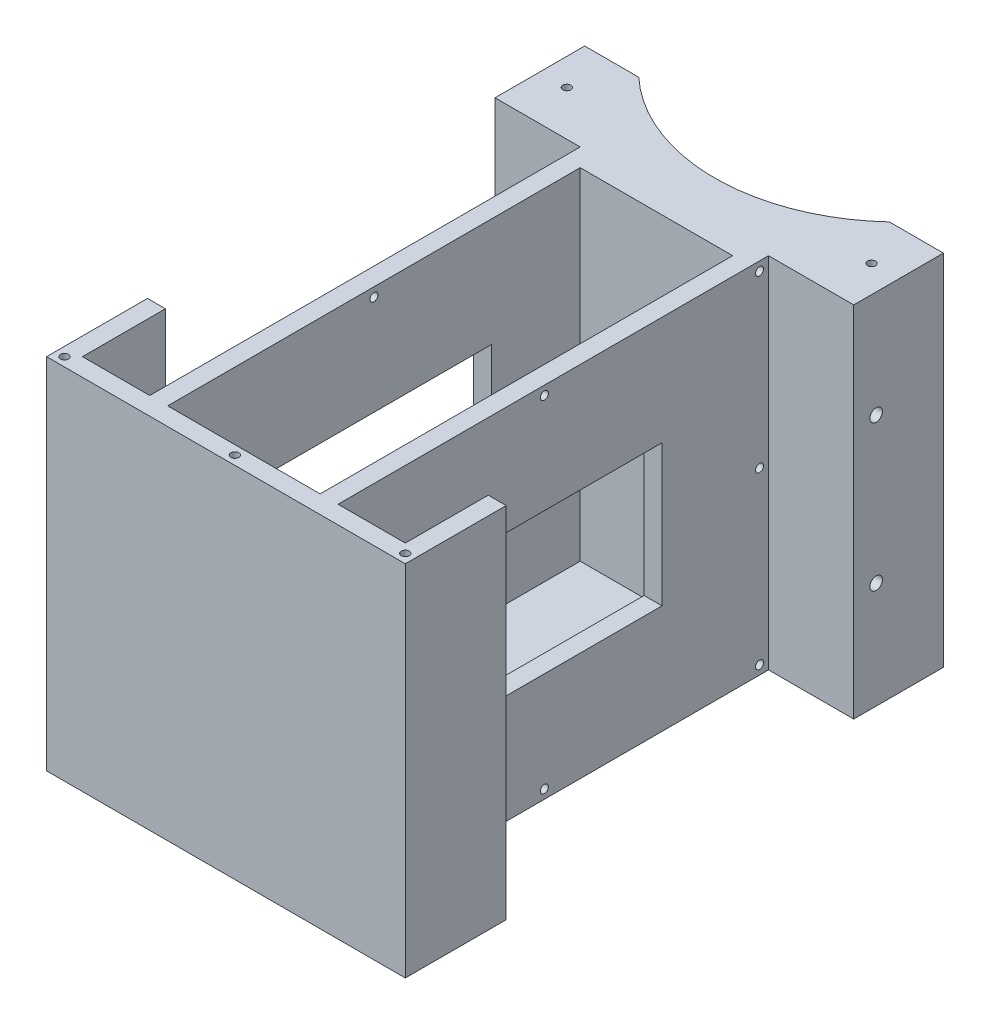
SolidWorks part; units mm, degrees
ref_plane "정면" through (0, 0, 0) normal (0, 0, 1) x (1, 0, 0)
ref_plane "윗면" through (0, 0, 0) normal (0, 1, 0) x (1, 0, 0)
ref_plane "우측면" through (0, 0, 0) normal (1, 0, 0) x (0, 0, -1)
ref_plane "평면1" through (0, 80, 0) normal (0, 1, 0) x (1, 0, 0)
sketch "스케치1" plane through (0, 80, 0) normal (0, 1, 0) x (1, 0, 0)
  line L0 (40, 60) -> (-40, 60)
  line L1 (-40, 60) -> (-40, -60)
  line L2 (-40, -60) -> (40, -60)
  line L3 (40, -60) -> (40, 60)
extrude "보스-돌출1" add sketch "스케치1" against normal blind 80
sketch "스케치2" plane through (0, 0, 0) normal (0, -1, 0) x (1, 0, 0)
  line L0 (-40, -40) -> (-21, -40)
  line L1 (-21, -40) -> (-21, 60)
  line L2 (-21, 60) -> (-40, 60)
  line L3 (-40, 60) -> (-40, -40)
extrude "컷-돌출1" cut sketch "스케치2" against normal through all
sketch "스케치3" plane through (0, 0, 0) normal (0, -1, 0) x (1, 0, 0)
  line L0 (21, 60) -> (21, -40)
  line L1 (21, -40) -> (40, -40)
  line L2 (40, -40) -> (40, 60)
  line L3 (40, 60) -> (21, 60)
extrude "컷-돌출2" cut sketch "스케치3" against normal through all
sketch "스케치4" plane through (0, 0, 0) normal (0, -1, 0) x (1, 0, 0)
  line L0 (-27.9464, -60) -> (27.9464, -60)
  arc A0 (27.9464, -60) -> (-27.9464, -60) centre (0, -90) ccw
extrude "컷-돌출3" cut sketch "스케치4" against normal through all
sketch "스케치5" plane through (0, 80, 0) normal (0, 1, 0) x (-1, 0, 0)
  line L0 (17, 56) -> (-17, 56)
  line L1 (-17, 56) -> (-17, -36)
  line L2 (-17, -36) -> (17, -36)
  line L3 (17, -36) -> (17, 56)
extrude "컷-돌출4" cut sketch "스케치5" against normal blind 76
sketch "스케치6" plane through (21, 0, 0) normal (1, 0, 0) x (0, 0, -1)
  line L0 (-34.75, 24.25) -> (14.75, 24.25)
  line L1 (14.75, 24.25) -> (14.75, 55.75)
  line L2 (14.75, 55.75) -> (-34.75, 55.75)
  line L3 (-34.75, 55.75) -> (-34.75, 24.25)
  line L4 (55, 80) -> (-55, 80) construction
  line L5 (40, 80) -> (40, 0) construction
  dimension "D1" = 31.5
  dimension "D2" = 49.5
  dimension "D3" = 24.25
  dimension "D4" = 25.25
extrude "컷-돌출5" cut sketch "스케치6" against normal up to next
sketch "스케치7" plane through (-21, 0, 0) normal (-1, 0, 0) x (0, 0, 1)
  line L0 (33.25, 55.75) -> (-16.25, 55.75)
  line L1 (-16.25, 55.75) -> (-16.25, 24.25)
  line L2 (-16.25, 24.25) -> (33.25, 24.25)
  line L3 (33.25, 24.25) -> (33.25, 55.75)
  line L4 (-40, 0) -> (60, 0) construction
  line L5 (-40, 80) -> (60, 80) construction
  line L7 (60, 80) -> (60, 0) construction
  dimension "D1" = 31.5
  dimension "D2" = 49.5
  dimension "D3" = 24.25
  dimension "D4" = 80
  dimension "D5" = 26.75
extrude "컷-돌출6" cut sketch "스케치7" against normal through all
hole_wizard "Ø1.8 (1.8) 지름 구멍5" positions "스케치9" profile "스케치8" hole size "Ø1.8" standard "Ansi Metric" end condition up to next
sketch "스케치9" plane through (-21, 0, 0) normal (-1, 0, 0) x (0, 0, 1)
  point P0 (10, 78)
sketch "스케치8" plane through (-21, 78, 10) normal (0, 1, 0) x (0, 0, 1)
  line L0 (0, 0) -> (0, 4)
  line L1 (0, 4) -> (0.9, 4)
  line L2 (0.9, 4) -> (0.9, 0)
  line L5 (0.9, 0) -> (0, 0)
  line L11 (0, -6.35) -> (0, 107.95) construction
  dimension "관통 구멍 지름" = 1.8
  dimension "관통 구멍 깊이" = 4
hole_wizard "Ø16.0 (16) 지름 구멍1" positions "스케치11" profile "스케치10" hole size "Ø16.0" standard "Ansi Metric" end condition through all
sketch "스케치11" plane through (0, 0, 0) normal (0, -1, 0) x (-1, 0, 0)
  point P0 (0, -22)
sketch "스케치10" plane through (0, 0, 22) normal (1, 0, 0) x (0, 0, -1)
  line L0 (0, 0) -> (0, 80)
  line L1 (0, 80) -> (8, 80)
  line L2 (8, 80) -> (8, 0)
  line L5 (8, 0) -> (0, 0)
  line L11 (0, -6.35) -> (0, 107.95) construction
  dimension "관통 구멍 지름" = 16
  dimension "관통 구멍 깊이" = 80
hole_wizard "Ø1.8 (1.8) 지름 구멍4" positions "스케치13" profile "스케치12" hole size "Ø1.8" standard "Ansi Metric"
sketch "스케치13" plane through (-21, 0, 0) normal (-1, 0, 0) x (0, 0, 1)
  point P0 (-38, 78)
  point P1 (-38, 40)
  point P2 (-38, 2)
  point P3 (10, 2)
sketch "스케치12" plane through (-21, 78, -38) normal (0, 1, 0) x (0, 0, 1)
  line L0 (0, 0) -> (0, 4.5408)
  line L1 (0, 4.5408) -> (0.9, 4)
  line L2 (0.9, 4) -> (0.9, 0)
  line L5 (0.9, 0) -> (0, 0)
  line L10 (0, 4.5408) -> (-0.9, 4) construction
  line L11 (0, -6.35) -> (0, 107.95) construction
  dimension "구멍 지름" = 1.8
  dimension "구멍 깊이" = 4
  dimension "드릴 각도" = 118
hole_wizard "Ø1.8 (1.8) 지름 구멍3" positions "스케치15" profile "스케치14" hole size "Ø1.8" standard "Ansi Metric" end condition through all
sketch "스케치15" plane through (21, 0, 0) normal (1, 0, 0) x (0, 0, -1)
  point P0 (-10, 78)
sketch "스케치14" plane through (21, 78, 10) normal (0, 1, 0) x (0, 0, -1)
  line L0 (0, 0) -> (0, 61)
  line L1 (0, 61) -> (0.9, 61)
  line L2 (0.9, 61) -> (0.9, 0)
  line L5 (0.9, 0) -> (0, 0)
  line L11 (0, -6.35) -> (0, 107.95) construction
  dimension "관통 구멍 지름" = 1.8
  dimension "관통 구멍 깊이" = 61
hole_wizard "Ø1.8 (1.8) 지름 구멍1" positions "스케치17" profile "스케치16" hole size "Ø1.8" standard "Ansi Metric"
sketch "스케치17" plane through (0, 80, 0) normal (0, 1, 0) x (1, 0, 0)
  point P0 (33.9732, 50)
  point P1 (-33.9732, 50)
sketch "스케치16" plane through (33.9732, 80, -50) normal (1, 0, 0) x (0, 0, 1)
  line L0 (0, 0) -> (0, 5.7408)
  line L1 (0, 5.7408) -> (0.9, 5.2)
  line L2 (0.9, 5.2) -> (0.9, 0)
  line L5 (0.9, 0) -> (0, 0)
  line L10 (0, 5.7408) -> (-0.9, 5.2) construction
  line L11 (0, -6.35) -> (0, 107.95) construction
  dimension "구멍 지름" = 1.8
  dimension "구멍 깊이" = 5.2
  dimension "드릴 각도" = 118
hole_wizard "Ø1.8 (1.8) 지름 구멍2" positions "스케치19" profile "스케치18" hole size "Ø1.8" standard "Ansi Metric"
sketch "스케치19" plane through (21, 0, 0) normal (1, 0, 0) x (0, 0, -1)
  point P0 (38, 78)
  point P1 (38, 40)
  point P2 (38, 2)
  point P3 (-10, 2)
sketch "스케치18" plane through (21, 78, -38) normal (0, 1, 0) x (0, 0, -1)
  line L0 (0, 0) -> (0, 4.5408)
  line L1 (0, 4.5408) -> (0.9, 4)
  line L2 (0.9, 4) -> (0.9, 0)
  line L5 (0.9, 0) -> (0, 0)
  line L10 (0, 4.5408) -> (-0.9, 4) construction
  line L11 (0, -6.35) -> (0, 107.95) construction
  dimension "구멍 지름" = 1.8
  dimension "구멍 깊이" = 4
  dimension "드릴 각도" = 118
sketch "스케치20" plane through (0, 80, 0) normal (0, 1, 0) x (1, 0, 0)
  line L0 (40, 40) -> (40, -101.7044) construction
  line L1 (-40, 60) -> (-40, 40) construction
  line L2 (21, -60) -> (55.4449, -60) construction
  line L3 (55.4449, -60) -> (-63.6399, -60) construction
  line L4 (40, 40) -> (40, 60) construction
  line L5 (40, -37.5) -> (36, -37.5)
  line L6 (40, -37.5) -> (40, -60)
  line L7 (40, -60) -> (-40, -60)
  line L8 (-40, -37.5) -> (-40, -60)
  line L9 (40, -37.5) -> (-40, -60) construction
  line L10 (40, -60) -> (-40, -37.5) construction
  line L12 (36, -37.5) -> (36, -56)
  line L13 (36, -56) -> (-36, -56)
  line L14 (-36, -56) -> (-36, -37.5)
  line L15 (-36, -37.5) -> (-40, -37.5)
  point P10 (0, -48.75)
  point P17 (40, 50)
  dimension "D1" = 0
  dimension "D2" = 80
  dimension "D3" = 0
  dimension "D4" = 4
  dimension "D5" = 4
  dimension "D6" = 4
  dimension "D7" = 22.5
  dimension "D8" = 22.5
  dimension "D9" = 80
extrude "보스-돌출2" add sketch "스케치20" against normal up to surface (80 mm away) up to face at (0, 0, -26.9)
sketch "스케치21" plane through (-40, 0, 0) normal (-1, 0, 0) x (0, 0, 1)
  line L0 (-40, 80) -> (-40, 0) construction
  line L1 (-50, 60) -> (-40, 60) construction
  line L2 (-50, 60) -> (-50, 20) construction
  line L3 (-50, 20) -> (-40, 20) construction
  line L4 (-40, 60) -> (-40, 20) construction
  line L5 (-60, 0) -> (-60, 80) construction
  circle A0 centre (23.2187, 40.5539) radius 22.5 construction
  circle A1 centre (-45, 23.75) radius 1.4
  circle A2 centre (-45, 56.25) radius 1.4
  point P8 (-50, 40)
  point P11 (-60, 40)
  point P18 (-46.7249, 20)
  dimension "D1" = 45
  dimension "D5" = 2.8
  dimension "D6" = 2.8
  dimension "D9" = 3.75
  dimension "D10" = 3.75
  dimension "D2" = 0
  dimension "D3" = 40
  dimension "D4" = 10
  dimension "D7" = 5
  dimension "D8" = 5
extrude "컷-돌출7" cut sketch "스케치21" against normal blind 8
sketch "스케치22" plane through (40, 0, 0) normal (1, 0, 0) x (0, 0, -1)
  line L0 (40, 80) -> (40, 0) construction
  line L1 (40, 20) -> (50, 20) construction
  line L2 (40, 20) -> (40, 60) construction
  line L3 (40, 60) -> (50, 60) construction
  line L4 (50, 20) -> (50, 60) construction
  line L5 (40, 0) -> (60, 0) construction
  circle A0 centre (45, 23.75) radius 1.4
  circle A1 centre (45, 56.25) radius 1.4
  dimension "D4" = 2.8
  dimension "D5" = 2.8
  dimension "D6" = 3.75
  dimension "D7" = 3.75
  dimension "D8" = 5
  dimension "D9" = 5
  dimension "D1" = 10
  dimension "D2" = 40
  dimension "D3" = 20
extrude "컷-돌출8" cut sketch "스케치22" against normal blind 8
sketch "스케치23" plane through (0, 80, 0) normal (0, 1, 0) x (1, 0, 0)
  line L0 (-40, -37.5) -> (-40, -60) construction
  line L2 (-40, -60) -> (40, -60) construction
  line L3 (40, -60) -> (40, -37.5) construction
  circle A0 centre (-38, -58) radius 0.9
  circle A1 centre (0, -58) radius 0.9
  circle A2 centre (38, -58) radius 0.9
  point P10 (-38.1076, -60)
  dimension "D1" = 1.8
  dimension "D2" = 1.8
  dimension "D3" = 1.8
  dimension "D5" = 2
  dimension "D6" = 2
  dimension "D7" = 40
  dimension "D8" = 2
  dimension "D9" = 2
  dimension "D4" = 2
extrude "컷-돌출9" cut sketch "스케치23" against normal blind 2
